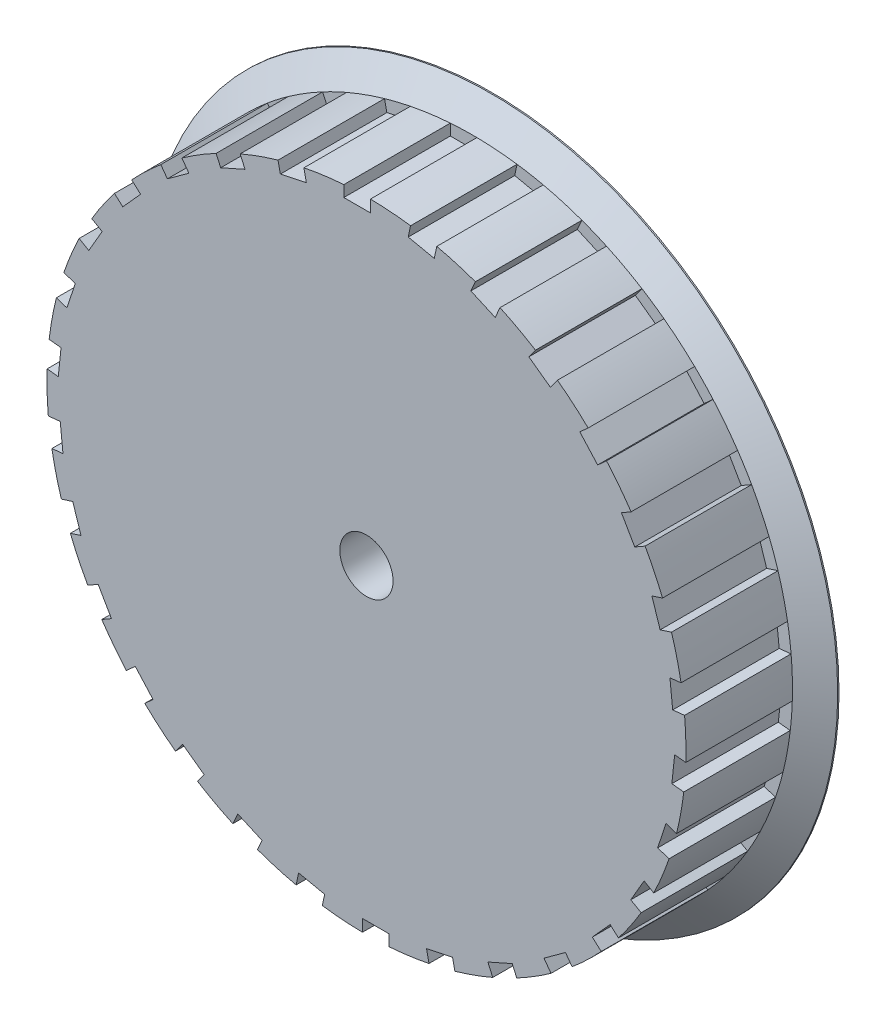
SolidWorks part; units mm, degrees
ref_plane "Front Plane" through (0, 0, 0) normal (0, 0, 1) x (1, 0, 0)
ref_plane "Top Plane" through (0, 0, 0) normal (0, 1, 0) x (1, 0, 0)
ref_plane "Right Plane" through (0, 0, 0) normal (1, 0, 0) x (0, 0, -1)
sketch "Sketch1" plane through (0, 0, 0) normal (1, 0, 0) x (0, 0, -1)
  line L0 (-5.5, 0) -> (-5.5, 26)
  line L1 (-5.5, 26) -> (-5.4004, 26)
  line L2 (-5.4004, 26) -> (-4, 24)
  line L3 (-4, 24) -> (0, 24)
  line L4 (0, 24) -> (0, 0)
  line L5 (-5.5, 0) -> (0, 0)
  dimension "D1" = 26
  dimension "D2" = 125
  dimension "D3" = 4
revolve "Revolve1" add sketch "Sketch1" angle 360 about L5
mirror "Mirror1" about plane through (0, 0, 0) normal (0, 0, 1) of "Revolve1"
sketch "Sketch2" plane through (0, 0, 5.5) normal (0, 0, 1) x (1, 0, 0)
  circle A0 centre (0, 0) radius 2
  dimension "D1" = 4
extrude "Cut-Extrude1" cut sketch "Sketch2" against normal blind 34
sketch "Sketch3" plane through (0, 0, 0) normal (0, 0, 1) x (1, 0, 0)
  line L1 (-1.701, 26.9096) -> (0.299, 26.9096)
  line L2 (-1.701, 26.9096) -> (-1.701, 23.0994)
  line L3 (-1.701, 23.0994) -> (0.299, 23.0994)
  line L4 (0.299, 26.9096) -> (0.299, 23.0994)
  line L5 (-1.701, 26.9096) -> (0.299, 23.0994) construction
  line L6 (-1.701, 23.0994) -> (0.299, 26.9096) construction
  point P0 (-0.701, 25.0045)
  dimension "D1" = 2
  dimension "D2" = 3.8102
extrude "Cut-Extrude2" cut sketch "Sketch3" against normal blind 4 and the other way blind 4
pattern_circular "CirPattern1" count 30 over 360 about axis through (0, 0, 0) along (0, 0, 1) of "Cut-Extrude2"
sketch "Sketch4" plane through (0, 0, 5.5) normal (0, 0, 1) x (1, 0, 0)
  circle A0 centre (0, 0) radius 35.7617
extrude "Cut-Extrude3" cut sketch "Sketch4" against normal blind 1.5
